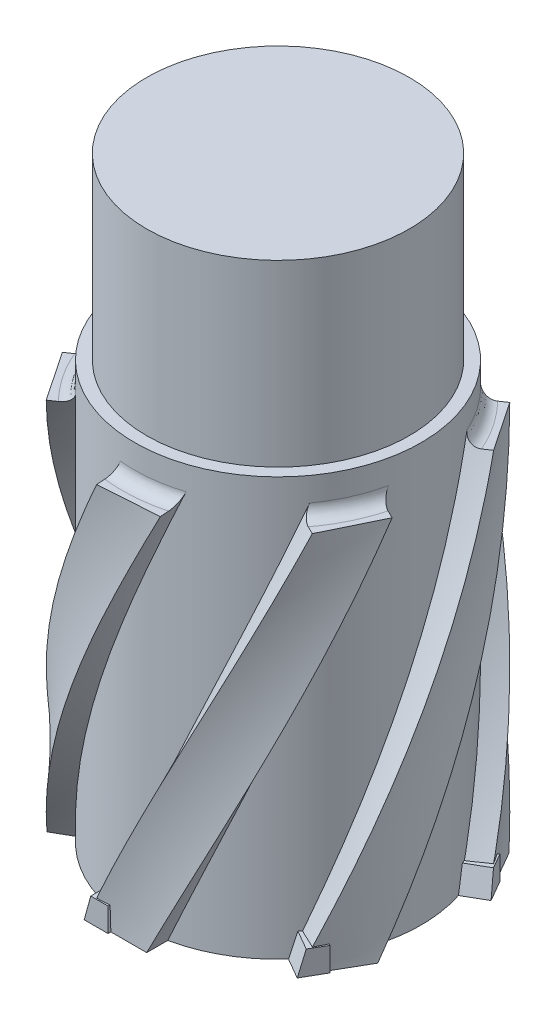
SolidWorks part; units mm, degrees
ref_plane "前视" through (0, 0, 0) normal (0, 0, 1) x (1, 0, 0)
ref_plane "上视" through (0, 0, 0) normal (0, 1, 0) x (1, 0, 0)
ref_plane "右视" through (0, 0, 0) normal (1, 0, 0) x (0, 0, -1)
sketch "草图1" plane through (0, 0, 0) normal (0, 1, 0) x (1, 0, 0)
  circle A0 centre (0, 0) radius 11
  dimension "D1" = 22
extrude "凸台-拉伸1" add sketch "草图1" along normal blind 50
sketch "草图2" plane through (0, 0, 0) normal (0, -1, 0) x (1, 0, 0)
  circle A0 centre (0, 0) radius 12
  dimension "D1" = 24
extrude "凸台-拉伸2" add sketch "草图2" against normal blind 35
sketch "草图3" plane through (0, 0, 0) normal (0, -1, 0) x (1, 0, 0)
  circle A1 centre (0, 0) radius 12
  circle A2 centre (0, 0) radius 12
  dimension "D1" = 0
curve "螺旋线/涡状线1" pitch 180 height 32 turns 0.1778
sketch "草图4" plane through (0, 0, 0) normal (0, -1, 0) x (1, 0, 0)
  line L1 (-2.5, -10.5) -> (2.5, -10.5)
  line L2 (-2.5, -10.5) -> (-2.5, -13.5)
  line L3 (-2.5, -13.5) -> (2.5, -13.5)
  line L4 (2.5, -10.5) -> (2.5, -13.5)
  line L5 (-2.5, -10.5) -> (2.5, -13.5) construction
  line L6 (-2.5, -13.5) -> (2.5, -10.5) construction
  circle A0 centre (0, 0) radius 12 construction
  point P0 (0, -12)
  dimension "D1" = 5
  dimension "D2" = 3
sweep "扫描1" add profiles "草图4" path "螺旋线/涡状线1"
fillet "圆角1" radius 1 1 edges
ref_plane "基准面1" through (2.5, 0, 0) normal (1, 0, 0) x (0, 0, -1)
pattern_circular "阵列(圆周)8" count 6 over 360 about axis through (0, 35, 0) along (0, -1, 0) of "扫描1", "圆角1"
sketch "草图6" plane through (2.5, 0, 0) normal (1, 0, 0) x (0, 0, -1)
  line L0 (13.7367, 0) -> (13.7367, 2)
  line L1 (13.7367, 2) -> (11.7367, 2)
  line L2 (11.7367, 2) -> (11.7367, 0)
  line L3 (11.7367, 0) -> (13.7367, 0)
  dimension "D1" = 2
  dimension "D2" = 2
extrude "凸台-拉伸3" add sketch "草图6" against normal blind 2 separate body
sketch "草图7" plane through (0, 0, -13.7367) normal (0, 0, -1) x (-1, 0, 0)
  line L0 (-2.5, 0) -> (-1.9486, 2)
  line L1 (-2.5, 50) -> (-2.5, -50) construction
  line L2 (-0.5, 2) -> (-2.5, 2) construction
  line L3 (-1.9486, 2) -> (-2.5, 2)
  line L4 (-2.5, 2) -> (-2.5, 0)
extrude "切除-拉伸2" cut sketch "草图7" against normal blind 2
sketch "草图5" plane through (0, 0, 0) normal (0, -1, 0) x (1, 0, 0)
  circle A0 centre (0, 0) radius 10
  dimension "D1" = 20
extrude "切除-拉伸1" cut sketch "草图5" against normal blind 48
pattern_circular "阵列(圆周)4" count 6 over 360 about axis through (0, 0, 0) along (0, 1, 0) of bodies 110 106
